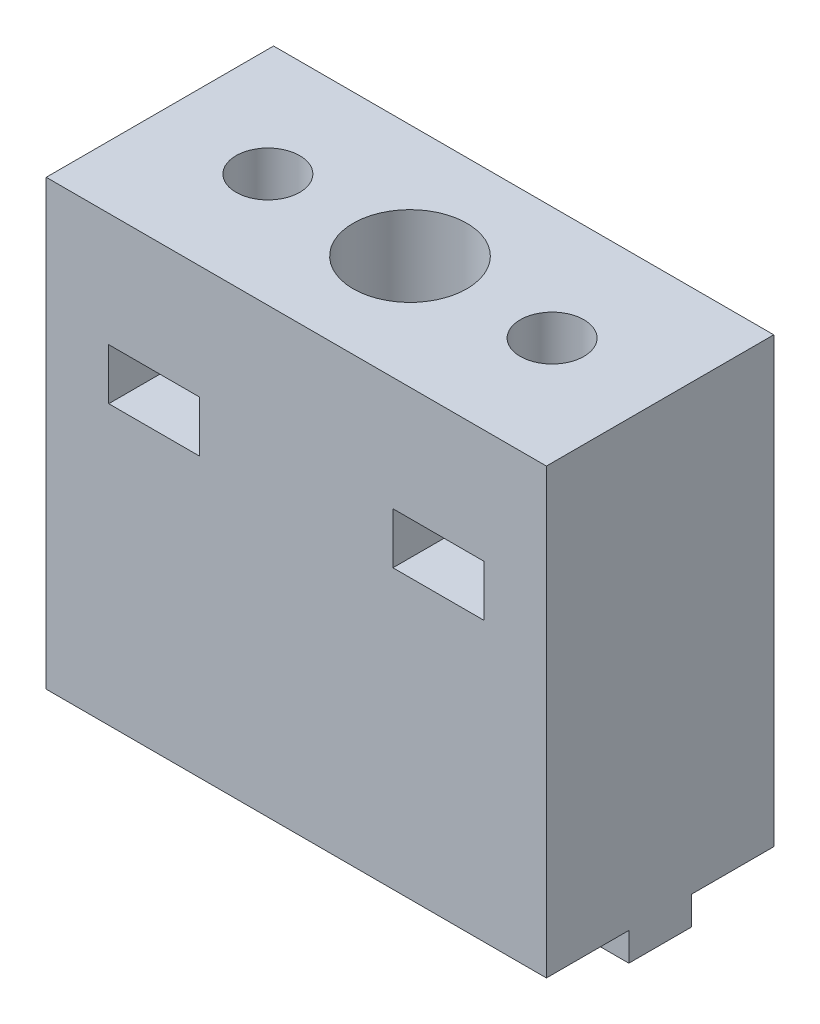
SolidWorks part; units mm, degrees
ref_plane "Front Plane" through (0, 0, 0) normal (0, 0, 1) x (1, 0, 0)
ref_plane "Top Plane" through (0, 0, 0) normal (0, 1, 0) x (1, 0, 0)
ref_plane "Right Plane" through (0, 0, 0) normal (1, 0, 0) x (0, 0, -1)
sketch "Sketch1" plane through (0, 0, 0) normal (0, 1, 0) x (1, 0, 0)
  line L1 (-0.6968, 0) -> (43.3032, 0)
  line L2 (-0.6968, 0) -> (-0.6968, 20)
  line L3 (-0.6968, 20) -> (43.3032, 20)
  line L4 (43.3032, 0) -> (43.3032, 20)
  dimension "D1" = 20
  dimension "D2" = 44
extrude "Boss-Extrude1" add sketch "Sketch1" along normal blind 39
sketch "Sketch3" plane through (0, 0, 0) normal (0, -1, 0) x (1, 0, 0)
  line L0 (43.3032, 0) -> (43.3032, -20) construction
  line L1 (43.3032, -12.75) -> (-0.6968, -12.75)
  line L2 (43.3032, -12.75) -> (43.3032, -7.25)
  line L3 (43.3032, -7.25) -> (-0.6968, -7.25)
  line L4 (-0.6968, -12.75) -> (-0.6968, -7.25)
  line L5 (-0.6968, -20) -> (-0.6968, 0) construction
  line L6 (43.3032, -20) -> (-0.6968, -20) construction
  dimension "D1" = 5.5
  dimension "D2" = 7.25
extrude "Boss-Extrude5" add sketch "Sketch3" along normal blind 2.5
sketch "Sketch2" plane through (0, 39, 0) normal (0, 1, 0) x (1, 0, 0)
  line L0 (43.3032, 20) -> (-0.6968, 20) construction
  line L1 (-0.6968, 20) -> (-0.6968, 0) construction
  line L2 (43.3032, 0) -> (43.3032, 20) construction
  circle A0 centre (8.8032, 10) radius 2.8
  circle A1 centre (33.8032, 10) radius 2.8
  circle A2 centre (21.3032, 10) radius 2.8
  dimension "D1" = 5.6
  dimension "D2" = 5.6
  dimension "D3" = 5.6
  dimension "D4" = 22
  dimension "D5" = 10
  dimension "D6" = 10
  dimension "D7" = 25
  dimension "D9" = 9.5
extrude "Cut-Extrude1" cut sketch "Sketch2" against normal through all
sketch "Sketch4" plane through (0, 39, 0) normal (0, 1, 0) x (1, 0, 0)
  line L0 (-0.6968, 0) -> (43.3032, 0) construction
  line L1 (-0.6968, 20) -> (-0.6968, 0) construction
  circle A0 centre (21.3032, 10) radius 5
  dimension "D1" = 10
  dimension "D2" = 10
  dimension "D3" = 22
extrude "Cut-Extrude2" cut sketch "Sketch4" against normal offset from surface (34 mm away) 5 up to face at (21.3032, 0, -5.785)
sketch "Sketch5" plane through (0, 0, -20) normal (0, 0, -1) x (-1, 0, 0)
  line L1 (-37.8032, 24.5) -> (-29.8032, 24.5)
  line L2 (-37.8032, 24.5) -> (-37.8032, 29)
  line L3 (-37.8032, 29) -> (-29.8032, 29)
  line L4 (-29.8032, 24.5) -> (-29.8032, 29)
  line L5 (-12.8032, 24.5) -> (-4.8032, 24.5)
  line L6 (-12.8032, 24.5) -> (-12.8032, 29)
  line L7 (-12.8032, 29) -> (-4.8032, 29)
  line L8 (-4.8032, 24.5) -> (-4.8032, 29)
  line L9 (-43.3032, 39) -> (0.6968, 39) construction
  line L10 (-43.3032, 39) -> (-43.3032, 0) construction
  line L11 (0.6968, 39) -> (0.6968, 0) construction
  dimension "D1" = 4.5
  dimension "D2" = 8
  dimension "D3" = 4.5
  dimension "D4" = 8
  dimension "D5" = 10
  dimension "D6" = 10
  dimension "D7" = 5.5
  dimension "D8" = 5.5
extrude "Cut-Extrude3" cut sketch "Sketch5" against normal through all
sketch "Sketch6" plane through (0, -2.5, 0) normal (0, -1, 0) x (1, 0, 0)
  line L0 (33.2765, -7.25) -> (21.83, -7.25) construction
  line L1 (26.3032, -7.25) -> (16.3032, -7.25)
  line L2 (26.3032, -7.25) -> (26.3032, -12.75)
  line L3 (26.3032, -12.75) -> (16.3032, -12.75)
  line L4 (16.3032, -7.25) -> (16.3032, -12.75)
  arc A0 (21.83, -12.75) -> (21.83, -7.25) centre (21.3032, -10) ccw construction
  arc A2 (20.7765, -7.25) -> (20.7765, -12.75) centre (21.3032, -10) ccw construction
  dimension "D1" = 5
  dimension "D2" = 5
extrude "Cut-Extrude4" cut sketch "Sketch6" against normal up to surface (2.5 mm away) up to face at (21.3032, 0, -14.215)
